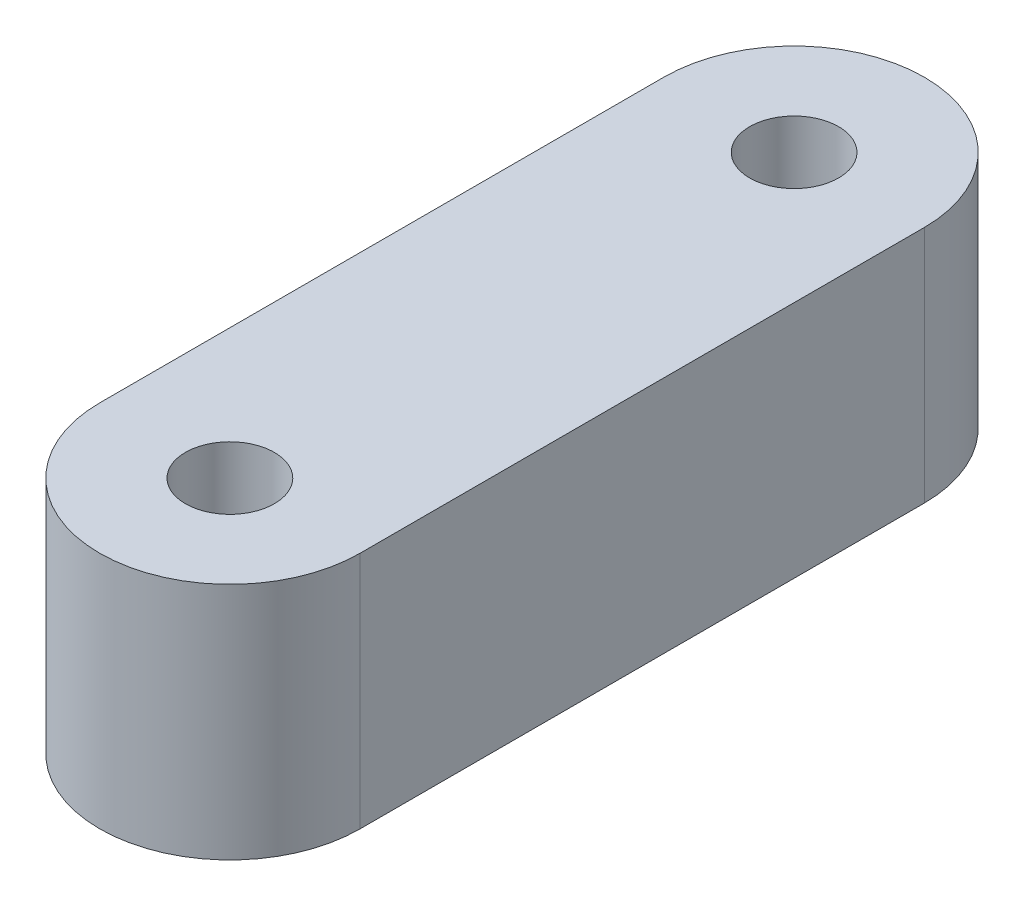
SolidWorks part; units mm, degrees
ref_plane "前视基准面" through (0, 0, 0) normal (0, 0, 1) x (1, 0, 0)
ref_plane "上视基准面" through (0, 0, 0) normal (0, 1, 0) x (1, 0, 0)
ref_plane "右视基准面" through (0, 0, 0) normal (1, 0, 0) x (0, 0, -1)
sketch "草图1" plane through (0, 0, 0) normal (0, 1, 0) x (1, 0, 0)
  line L0 (0, -13) -> (0, 13) construction
  line L1 (-6, -13) -> (-6, 13)
  line L2 (6, -13) -> (6, 13)
  arc A0 (-6, -13) -> (6, -13) centre (0, -13) ccw
  arc A1 (6, 13) -> (-6, 13) centre (0, 13) ccw
  point P2 (0, 0)
  dimension "D1" = 26
  dimension "D2" = 12
extrude "凸台-拉伸1" add sketch "草图1" along normal blind 11
sketch "草图2" plane through (0, 11, 0) normal (0, 1, 0) x (1, 0, 0)
  circle A0 centre (0, 13) radius 2.05
  circle A1 centre (0, -13) radius 2.05
  dimension "D1" = 13
  dimension "D3" = 4.1
  dimension "D4" = 4.1
  dimension "D5" = 0
  dimension "D6" = 0
  dimension "D2" = 13
extrude "切除-拉伸1" cut sketch "草图2" against normal through all
sketch "草图3" plane through (-6, 0, 0) normal (-1, 0, 0) x (0, 0, 1)
  line L0 (-13, 0) -> (13, 0) construction
  circle A0 centre (0, 5.5) radius 3.6
  dimension "D1" = 5.5
  dimension "D2" = 7.2
extrude "切除-拉伸2" cut sketch "草图3" against normal blind 10
